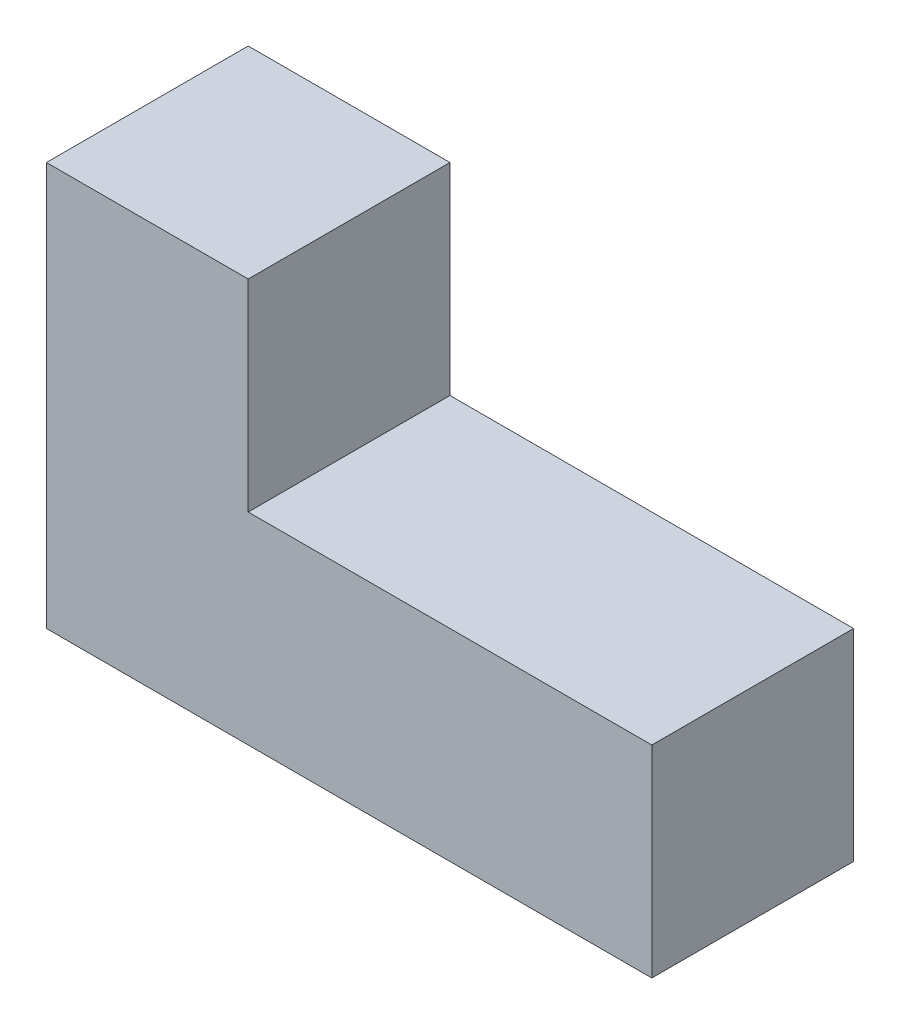
SolidWorks part; units mm, degrees
material "Cast Alloy Steel"
ref_plane "Front Plane" through (0, 0, 0) normal (0, 0, 1) x (1, 0, 0)
ref_plane "Top Plane" through (0, 0, 0) normal (0, 1, 0) x (1, 0, 0)
ref_plane "Right Plane" through (0, 0, 0) normal (1, 0, 0) x (0, 0, -1)
sketch "Sketch2" plane through (0, 0, 0) normal (0, 0, 1) x (1, 0, 0)
  line L0 (0, 0) -> (90, 0)
  line L1 (90, 0) -> (90, 30)
  line L2 (90, 30) -> (30, 30)
  line L3 (30, 30) -> (30, 60)
  line L4 (30, 60) -> (0, 60)
  line L5 (0, 60) -> (0, 0)
  dimension "D1" = 90
  dimension "D2" = 30
  dimension "D3" = 30
  dimension "D4" = 30
extrude "Boss-Extrude1" add sketch "Sketch2" along normal blind 30
